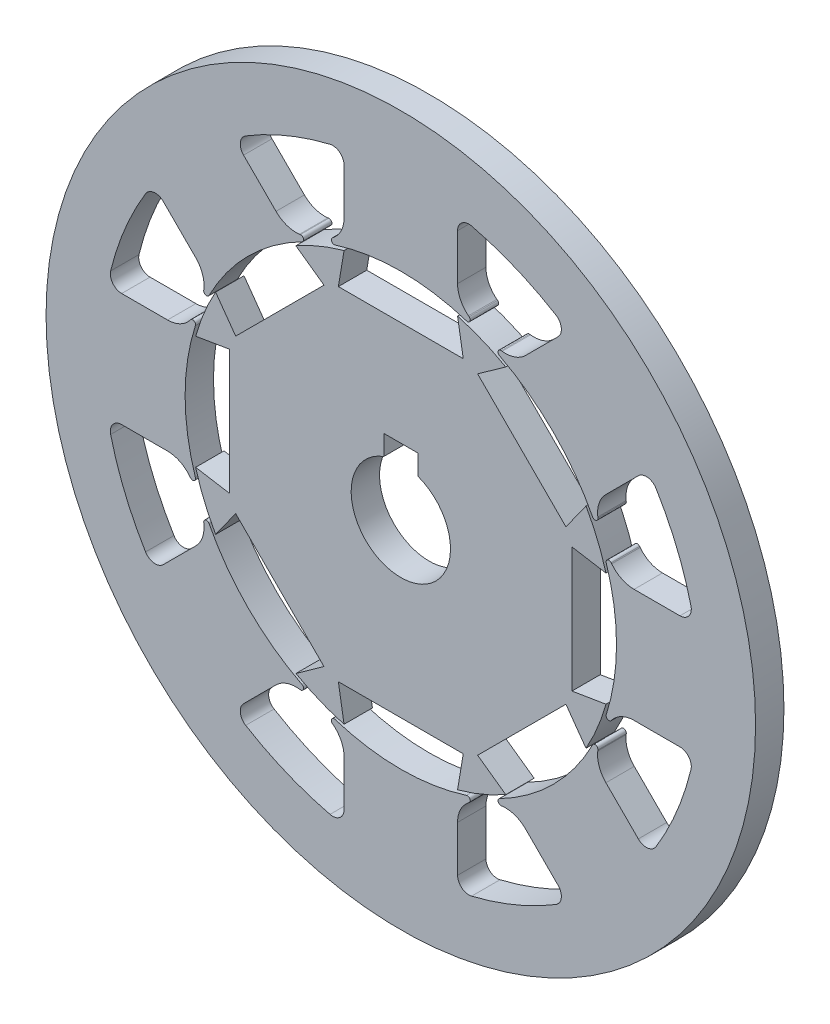
SolidWorks part; units mm, degrees
ref_plane "Ön Düzlem" through (0, 0, 0) normal (0, 0, 1) x (1, 0, 0)
ref_plane "Üst Düzlem" through (0, 0, 0) normal (0, 1, 0) x (1, 0, 0)
ref_plane "Sağ Düzlem" through (0, 0, 0) normal (1, 0, 0) x (0, 0, -1)
sketch "Çizim1" plane through (0, 0, 0) normal (0, 0, 1) x (1, 0, 0)
  line L0 (-20, 72.2842) -> (-22, 60.2842)
  line L5 (-22, 60.2842) -> (22, 60.2842)
  line L6 (22, 60.2842) -> (20, 72.2842)
  line L7 (58.1837, 27.071) -> (65.2548, 36.9705)
  line L8 (27.071, 58.1837) -> (58.1837, 27.071)
  line L9 (36.9705, 65.2548) -> (27.071, 58.1837)
  line L10 (60.2842, -22) -> (72.2842, -20)
  line L11 (60.2842, 22) -> (60.2842, -22)
  line L12 (72.2842, 20) -> (60.2842, 22)
  line L13 (27.071, -58.1837) -> (36.9705, -65.2548)
  line L14 (58.1837, -27.071) -> (27.071, -58.1837)
  line L15 (65.2548, -36.9705) -> (58.1837, -27.071)
  line L16 (-22, -60.2842) -> (-20, -72.2842)
  line L17 (22, -60.2842) -> (-22, -60.2842)
  line L18 (20, -72.2842) -> (22, -60.2842)
  line L19 (-58.1837, -27.071) -> (-65.2548, -36.9705)
  line L20 (-27.071, -58.1837) -> (-58.1837, -27.071)
  line L21 (-36.9705, -65.2548) -> (-27.071, -58.1837)
  line L22 (-60.2842, 22) -> (-72.2842, 20)
  line L23 (-60.2842, -22) -> (-60.2842, 22)
  line L24 (-72.2842, -20) -> (-60.2842, -22)
  line L25 (-27.071, 58.1837) -> (-36.9705, 65.2548)
  line L26 (-58.1837, 27.071) -> (-27.071, 58.1837)
  line L27 (-65.2548, 36.9705) -> (-58.1837, 27.071)
  line L28 (43.9783, 72.2625) -> (55.4041, 83.6884)
  line L29 (-6, 23.5) -> (6, 23.5)
  line L30 (-6, 23.5) -> (-6, 16.4393)
  line L32 (6, 23.5) -> (6, 16.4393)
  line L34 (-20, 82.1946) -> (-20, 98.3532)
  line L36 (20, 82.1946) -> (20, 98.3532)
  line L37 (0, 0) -> (-6.697, 16.1679)
  line L38 (-24.0884, 74.1228) -> (-23.8384, 74.3184)
  line L39 (35.3797, 69.4459) -> (35.6947, 69.4074)
  line L40 (0, 0) -> (6.697, 16.1679)
  line L41 (24.0884, 74.1228) -> (23.8384, 74.3184)
  line L42 (69.4459, 35.3797) -> (69.4074, 35.6947)
  line L43 (72.2625, 43.9783) -> (83.6884, 55.4041)
  line L44 (82.1946, 20) -> (98.3532, 20)
  line L45 (74.1228, 24.0884) -> (74.3184, 23.8384)
  line L46 (74.1228, -24.0884) -> (74.3184, -23.8384)
  line L47 (82.1946, -20) -> (98.3532, -20)
  line L48 (72.2625, -43.9783) -> (83.6884, -55.4041)
  line L49 (69.4459, -35.3797) -> (69.4074, -35.6947)
  line L50 (35.3797, -69.4459) -> (35.6947, -69.4074)
  line L51 (43.9783, -72.2625) -> (55.4041, -83.6884)
  line L52 (20, -82.1946) -> (20, -98.3532)
  line L53 (24.0884, -74.1228) -> (23.8384, -74.3184)
  line L54 (-24.0884, -74.1228) -> (-23.8384, -74.3184)
  line L55 (-20, -82.1946) -> (-20, -98.3532)
  line L56 (-43.9783, -72.2625) -> (-55.4041, -83.6884)
  line L57 (-35.3797, -69.4459) -> (-35.6947, -69.4074)
  line L58 (-69.4459, -35.3797) -> (-69.4074, -35.6947)
  line L59 (-72.2625, -43.9783) -> (-83.6884, -55.4041)
  line L60 (-82.1946, -20) -> (-98.3532, -20)
  line L61 (-74.1228, -24.0884) -> (-74.3184, -23.8384)
  line L62 (-74.1228, 24.0884) -> (-74.3184, 23.8384)
  line L63 (-82.1946, 20) -> (-98.3532, 20)
  line L64 (-72.2625, 43.9783) -> (-83.6884, 55.4041)
  line L65 (-69.4459, 35.3797) -> (-69.4074, 35.6947)
  line L66 (-35.3797, 69.4459) -> (-35.6947, 69.4074)
  line L67 (-43.9783, 72.2625) -> (-55.4041, 83.6884)
  arc A0 (-65.2548, 36.9705) -> (-72.2842, 20) centre (0, 0) ccw
  arc A1 (-6, 16.4393) -> (6, 16.4393) centre (0, 0) ccw
  arc A2 (-20, 72.2842) -> (-36.9705, 65.2548) centre (0, 0) ccw
  arc A3 (36.9705, 65.2548) -> (20, 72.2842) centre (0, 0) ccw
  arc A4 (72.2842, 20) -> (65.2548, 36.9705) centre (0, 0) ccw
  arc A5 (65.2548, -36.9705) -> (72.2842, -20) centre (0, 0) ccw
  arc A6 (20, -72.2842) -> (36.9705, -65.2548) centre (0, 0) ccw
  arc A7 (-36.9705, -65.2548) -> (-20, -72.2842) centre (0, 0) ccw
  arc A8 (-72.2842, -20) -> (-65.2548, -36.9705) centre (0, 0) ccw
  arc A9 (23.1674, 72.3828) -> (-23.1674, 72.3828) centre (0, 0) ccw
  arc A10 (20, 82.1946) -> (23.8384, 74.3184) centre (30, 82.1946) ccw
  arc A11 (-23.8384, 74.3184) -> (-20, 82.1946) centre (-30, 82.1946) ccw
  arc A12 (24.0884, 74.1228) -> (23.1674, 72.3828) centre (23.4723, 73.3352) cw
  arc A13 (-24.0884, 74.1228) -> (-23.1674, 72.3828) centre (-23.4723, 73.3352) ccw
  circle A14 centre (0, 0) radius 125
  arc A15 (35.6947, 69.4074) -> (43.9783, 72.2625) centre (36.9072, 79.3336) ccw
  arc A16 (67.5642, 34.8005) -> (34.8005, 67.5642) centre (0, 0) ccw
  arc A17 (35.3797, 69.4459) -> (34.8005, 67.5642) centre (35.2584, 68.4532) ccw
  arc A18 (69.4459, 35.3797) -> (67.5642, 34.8005) centre (68.4532, 35.2584) cw
  arc A19 (72.2625, 43.9783) -> (69.4074, 35.6947) centre (79.3336, 36.9072) ccw
  arc A20 (74.3184, 23.8384) -> (82.1946, 20) centre (82.1946, 30) ccw
  arc A21 (72.3828, -23.1674) -> (72.3828, 23.1674) centre (0, 0) ccw
  arc A22 (74.1228, 24.0884) -> (72.3828, 23.1674) centre (73.3352, 23.4723) ccw
  arc A23 (74.1228, -24.0884) -> (72.3828, -23.1674) centre (73.3352, -23.4723) cw
  arc A24 (82.1946, -20) -> (74.3184, -23.8384) centre (82.1946, -30) ccw
  arc A25 (69.4074, -35.6947) -> (72.2625, -43.9783) centre (79.3336, -36.9072) ccw
  arc A26 (34.8005, -67.5642) -> (67.5642, -34.8005) centre (0, 0) ccw
  arc A27 (69.4459, -35.3797) -> (67.5642, -34.8005) centre (68.4532, -35.2584) ccw
  arc A28 (35.3797, -69.4459) -> (34.8005, -67.5642) centre (35.2584, -68.4532) cw
  arc A29 (43.9783, -72.2625) -> (35.6947, -69.4074) centre (36.9072, -79.3336) ccw
  arc A30 (23.8384, -74.3184) -> (20, -82.1946) centre (30, -82.1946) ccw
  arc A31 (-23.1674, -72.3828) -> (23.1674, -72.3828) centre (0, 0) ccw
  arc A32 (24.0884, -74.1228) -> (23.1674, -72.3828) centre (23.4723, -73.3352) ccw
  arc A33 (-24.0884, -74.1228) -> (-23.1674, -72.3828) centre (-23.4723, -73.3352) cw
  arc A34 (-20, -82.1946) -> (-23.8384, -74.3184) centre (-30, -82.1946) ccw
  arc A35 (-35.6947, -69.4074) -> (-43.9783, -72.2625) centre (-36.9072, -79.3336) ccw
  arc A36 (-67.5642, -34.8005) -> (-34.8005, -67.5642) centre (0, 0) ccw
  arc A37 (-35.3797, -69.4459) -> (-34.8005, -67.5642) centre (-35.2584, -68.4532) ccw
  arc A38 (-69.4459, -35.3797) -> (-67.5642, -34.8005) centre (-68.4532, -35.2584) cw
  arc A39 (-72.2625, -43.9783) -> (-69.4074, -35.6947) centre (-79.3336, -36.9072) ccw
  arc A40 (-74.3184, -23.8384) -> (-82.1946, -20) centre (-82.1946, -30) ccw
  arc A41 (-72.3828, 23.1674) -> (-72.3828, -23.1674) centre (0, 0) ccw
  arc A42 (-74.1228, -24.0884) -> (-72.3828, -23.1674) centre (-73.3352, -23.4723) ccw
  arc A43 (-74.1228, 24.0884) -> (-72.3828, 23.1674) centre (-73.3352, 23.4723) cw
  arc A44 (-82.1946, 20) -> (-74.3184, 23.8384) centre (-82.1946, 30) ccw
  arc A45 (-69.4074, 35.6947) -> (-72.2625, 43.9783) centre (-79.3336, 36.9072) ccw
  arc A46 (-34.8005, 67.5642) -> (-67.5642, 34.8005) centre (0, 0) ccw
  arc A47 (-69.4459, 35.3797) -> (-67.5642, 34.8005) centre (-68.4532, 35.2584) ccw
  arc A48 (-35.3797, 69.4459) -> (-34.8005, 67.5642) centre (-35.2584, 68.4532) cw
  arc A49 (-43.9783, 72.2625) -> (-35.6947, 69.4074) centre (-36.9072, 79.3336) ccw
  arc A50 (-89.9351, 54.653) -> (-102.2392, 24.9483) centre (0, 0) ccw
  arc A51 (-24.9483, 102.2392) -> (-54.653, 89.9351) centre (0, 0) ccw
  arc A52 (54.653, 89.9351) -> (24.9483, 102.2392) centre (0, 0) ccw
  arc A53 (102.2392, 24.9483) -> (89.9351, 54.653) centre (0, 0) ccw
  arc A54 (89.9351, -54.653) -> (102.2392, -24.9483) centre (0, 0) ccw
  arc A55 (24.9483, -102.2392) -> (54.653, -89.9351) centre (0, 0) ccw
  arc A56 (-54.653, -89.9351) -> (-24.9483, -102.2392) centre (0, 0) ccw
  arc A57 (-102.2392, -24.9483) -> (-89.9351, -54.653) centre (0, 0) ccw
  arc A58 (102.2392, 24.9483) -> (98.3532, 20) centre (98.3532, 24) cw
  arc A59 (54.653, -89.9351) -> (55.4041, -83.6884) centre (52.5757, -86.5168) ccw
  arc A60 (-54.653, -89.9351) -> (-55.4041, -83.6884) centre (-52.5757, -86.5168) cw
  arc A61 (-102.2392, -24.9483) -> (-98.3532, -20) centre (-98.3532, -24) cw
  arc A62 (-89.9351, -54.653) -> (-83.6884, -55.4041) centre (-86.5168, -52.5757) ccw
  arc A63 (-20, -98.3532) -> (-24.9483, -102.2392) centre (-24, -98.3532) cw
  arc A64 (24.9483, -102.2392) -> (20, -98.3532) centre (24, -98.3532) cw
  arc A65 (89.9351, -54.653) -> (83.6884, -55.4041) centre (86.5168, -52.5757) cw
  arc A66 (98.3532, -20) -> (102.2392, -24.9483) centre (98.3532, -24) cw
  arc A67 (83.6884, 55.4041) -> (89.9351, 54.653) centre (86.5168, 52.5757) cw
  arc A68 (54.653, 89.9351) -> (55.4041, 83.6884) centre (52.5757, 86.5168) cw
  arc A69 (20, 98.3532) -> (24.9483, 102.2392) centre (24, 98.3532) cw
  arc A70 (-102.2392, 24.9483) -> (-98.3532, 20) centre (-98.3532, 24) ccw
  arc A71 (-89.9351, 54.653) -> (-83.6884, 55.4041) centre (-86.5168, 52.5757) cw
  arc A72 (-54.653, 89.9351) -> (-55.4041, 83.6884) centre (-52.5757, 86.5168) ccw
  arc A73 (-24.9483, 102.2392) -> (-20, 98.3532) centre (-24, 98.3532) cw
  point P35 (0, 0)
  point P156 (0, 0)
  point P179 (20, 103.3212)
  point P188 (-20, 103.3212)
  dimension "D8" = 35
  dimension "D6" = 152
  dimension "D9" = 1
  dimension "D13" = 10
  dimension "D12" = 250
  dimension "D15" = 4
  dimension "D1" = 44
  dimension "D2" = 40
  dimension "D3" = 2
  dimension "D4" = 2
  dimension "D5" = 8
  dimension "D7" = 12
  dimension "D10" = 12
  dimension "D11" = 40
  dimension "D14" = 8
extrude "Yükseklik-Ekstrüzyon1" add sketch "Çizim1" along normal blind 10 contours A14 A51 A73 L34 A11 L38 A13 A9 A12 L41 A10 L36 A69 A52 A68 L28 A15 L39 A17 A16 A18 L42 A19 L43 A67 A53 A58 L44 A20 L45 A22 A21 A23 L46 A24 L47 A66 A54 A65 L48 A25 L49 A27 A26 A28 L50 A29 L51 A59 A55 | L24 A8 L19 L20 L21 A7 L16 L17 L18 A6 L13 L14 L15 A5 L10 L11 L12 A4 L7 L8 L9 A3 L6 L5 L0 A2 L25 L26 L27 A0 L22 L23 A1 L30 L29 L32
